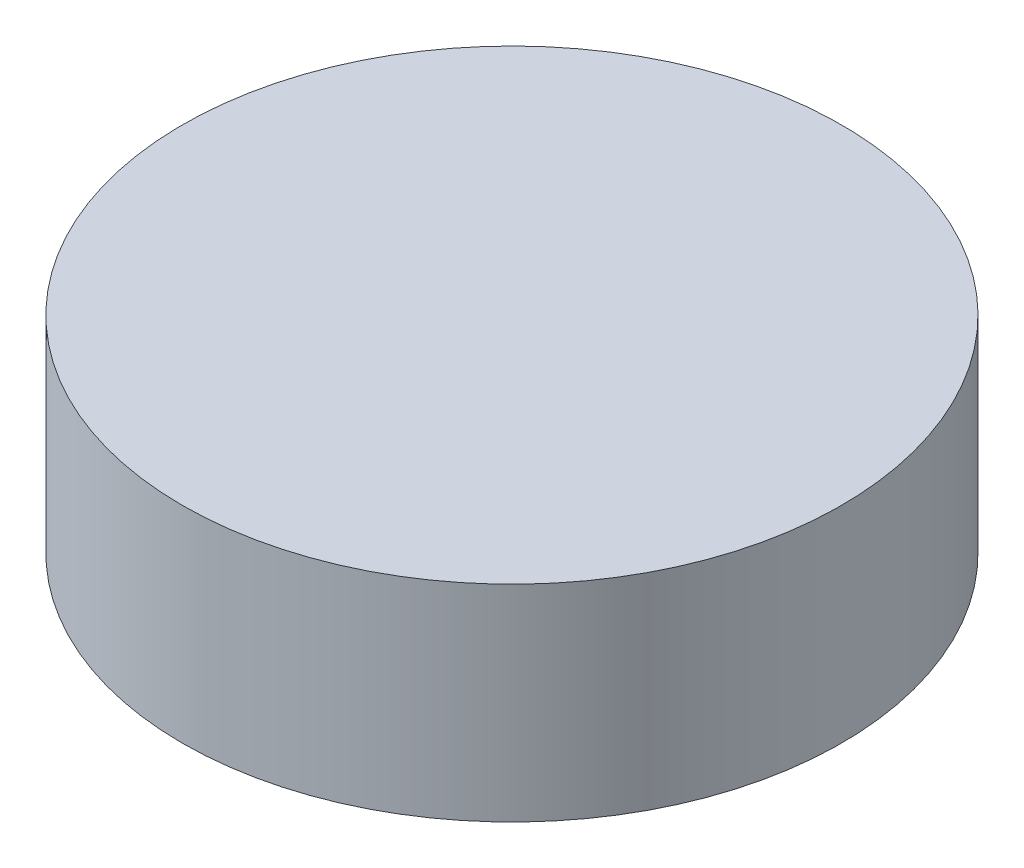
SolidWorks part; units mm, degrees
ref_plane "Front Plane" through (0, 0, 0) normal (0, 0, 1) x (1, 0, 0)
ref_plane "Top Plane" through (0, 0, 0) normal (0, 1, 0) x (1, 0, 0)
ref_plane "Right Plane" through (0, 0, 0) normal (1, 0, 0) x (0, 0, -1)
sketch "Magnet Sketch" plane through (0, 0, 0) normal (0, 1, 0) x (1, 0, 0)
  circle A0 centre (0, 0) radius 4
  dimension "Diameter" = 8
extrude "Magent Boss-Extrude" add sketch "Magnet Sketch" along normal blind 2.5
equation "\"Diameter@Magnet Sketch\" = 8mm"
